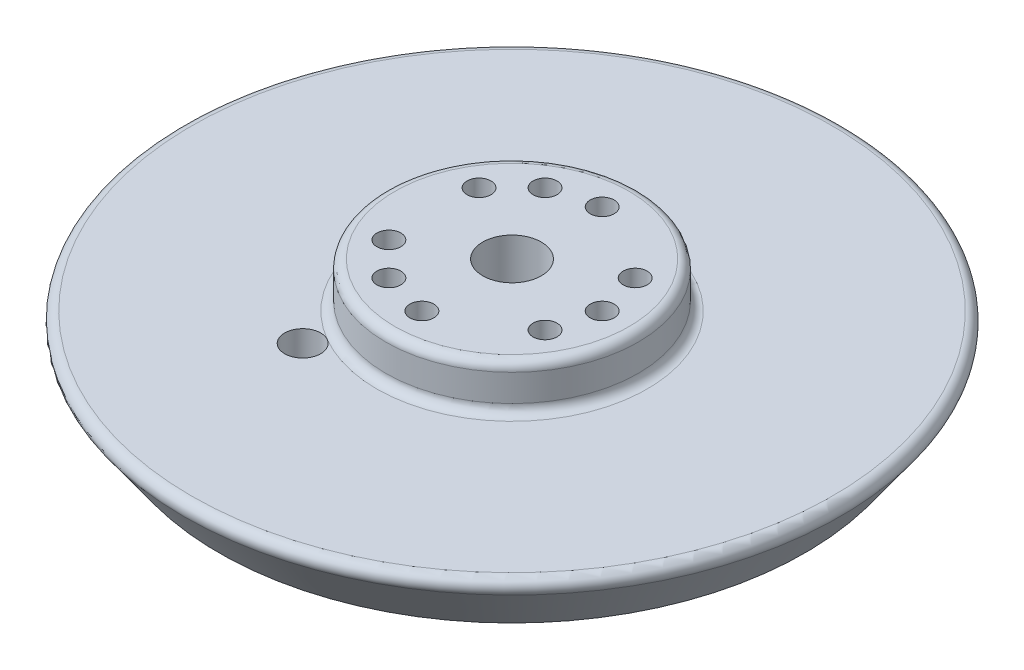
SolidWorks part; units mm, degrees
ref_plane "Plan de face" through (0, 0, 0) normal (0, 0, 1) x (1, 0, 0)
ref_plane "Plan de dessus" through (0, 0, 0) normal (0, 1, 0) x (1, 0, 0)
ref_plane "Plan de droite" through (0, 0, 0) normal (1, 0, 0) x (0, 0, -1)
sketch "Esquisse1" plane through (0, 0, 0) normal (0, 0, 1) x (1, 0, 0)
  line L0 (0, 0) -> (0, 21.4709) construction
  line L1 (14, -5) -> (37.5, -5)
  line L2 (37.5, -5) -> (32.5, -12)
  line L3 (32.5, -12) -> (0, -12)
  line L4 (0, 0) -> (14, 0)
  line L5 (14, 0) -> (14, -5)
  line L6 (0, 0) -> (0, -12)
  line L7 (0, -5) -> (14, -5) construction
  point P9 (0, -0.6303)
  point P11 (0, 0.6956)
  dimension "D1" = 14
  dimension "D2" = 37.5
  dimension "D3" = 32.5
  dimension "D4" = 7
  dimension "D5" = 5
revolve "Révolution1" add sketch "Esquisse1" angle 360 about L0
fillet "Congé1" radius 1 3 edges at (0, -5, -37.5) (0, 0, -14) (0, -5, -14)
sketch "Esquisse2" plane through (0, -12, 0) normal (0, -1, 0) x (1, 0, 0)
  line L0 (0, 0) -> (23.6151, 0) construction
  line L1 (0, 0) -> (-5, 8.6603) construction
  line L2 (-5, 8.6603) -> (-11.2949, 19.5634) construction
  circle A0 centre (0, 0) radius 3.25
  circle A1 centre (10, 0) radius 1.33
  circle A2 centre (-5, -8.6603) radius 1.33
  circle A3 centre (-5, 8.6603) radius 1.33
  circle A4 centre (-8.5, 14.7224) radius 2
  point P12 (0, 0)
  dimension "D1" = 6.5
  dimension "D2" = 2.66
  dimension "D3" = 10
  dimension "D5" = 4
  dimension "D6" = 17
  dimension "D4" = 3
extrude "Enlèv. mat.-Extru.1" cut sketch "Esquisse2" against normal up to next
chamfer "Chanfrein1" distance 2 angle 45 1 edges at (0, -12, -3.25)
sketch "Esquisse3" plane through (0, 0, 0) normal (0, 1, 0) x (1, 0, 0)
  line L0 (0, 0) -> (10, 0) construction
  line L1 (0, 0) -> (8.6603, 5) construction
  circle A1 centre (8.6603, 5) radius 1.33
  circle A2 centre (8.6603, -5) radius 1.33
  circle A3 centre (-8.6603, -5) radius 1.33
  circle A4 centre (0, -10) radius 1.33
  circle A5 centre (0, 10) radius 1.33
  circle A6 centre (-8.6603, 5) radius 1.33
  point P18 (0, 0)
  dimension "D3" = 2.66
  dimension "D1" = 30
  dimension "D2" = 10
  dimension "D4" = 3
extrude "Enlèv. mat.-Extru.2" cut sketch "Esquisse3" against normal up to surface (5 mm away) up to face at (-4.25, -5, 15.8612)
